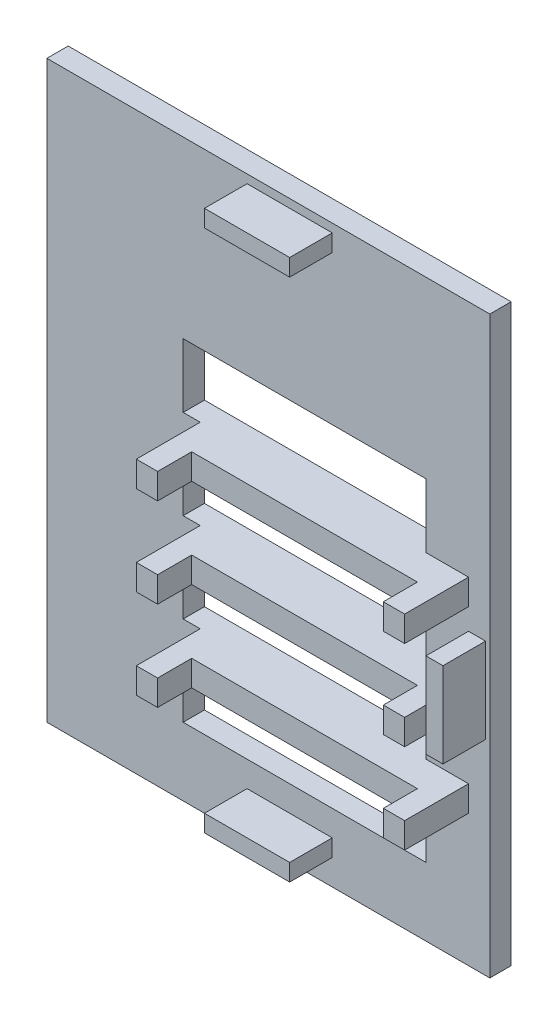
SolidWorks part; units mm, degrees
ref_plane "前基準面" through (0, 0, 0) normal (0, 0, 1) x (1, 0, 0)
ref_plane "上基準面" through (0, 0, 0) normal (0, 1, 0) x (1, 0, 0)
ref_plane "右基準面" through (0, 0, 0) normal (1, 0, 0) x (0, 0, -1)
sketch "草圖1" plane through (0, 0, 0) normal (0, 0, 1) x (1, 0, 0)
  line L17 (-17.8968, 14.4968) -> (86.1032, 14.4968)
  line L18 (-17.8968, 14.4968) -> (-17.8968, -120.5032)
  line L19 (-17.8968, -120.5032) -> (86.1032, -120.5032)
  line L20 (86.1032, 14.4968) -> (86.1032, -120.5032)
  dimension "D1" = 104
  dimension "D2" = 135
extrude "填料-伸長2" add sketch "草圖1" along normal blind 5
sketch "草圖2" plane through (0, 0, 5) normal (0, 0, 1) x (1, 0, 0)
  line L0 (86.1032, 14.4968) -> (-17.8968, 14.4968) construction
  line L1 (29.1032, 12.4968) -> (49.1032, 12.4968)
  line L2 (29.1032, 12.4968) -> (29.1032, 8.4968)
  line L3 (29.1032, 8.4968) -> (49.1032, 8.4968)
  line L4 (49.1032, 12.4968) -> (49.1032, 8.4968)
  line L10 (86.1032, -120.5032) -> (86.1032, 14.4968) construction
  line L11 (29.1032, -114.5032) -> (49.1032, -114.5032)
  line L12 (29.1032, -114.5032) -> (29.1032, -110.5032)
  line L13 (29.1032, -110.5032) -> (49.1032, -110.5032)
  line L14 (49.1032, -114.5032) -> (49.1032, -110.5032)
  line L15 (-17.8968, -120.5032) -> (86.1032, -120.5032) construction
  line L16 (-17.8968, 14.4968) -> (-17.8968, -120.5032) construction
  line L17 (85.1032, -52.5032) -> (81.1032, -52.5032)
  line L18 (85.1032, -52.5032) -> (85.1032, -72.5032)
  line L19 (85.1032, -72.5032) -> (81.1032, -72.5032)
  line L20 (81.1032, -52.5032) -> (81.1032, -72.5032)
  dimension "D2" = 20
  dimension "D3" = 4
  dimension "D4" = 67
  dimension "D5" = 4
  dimension "D6" = 20
  dimension "D7" = 20
  dimension "D8" = 4
  dimension "D9" = 6
  dimension "D10" = 47
  dimension "D11" = 2
  dimension "D12" = 1
  dimension "D13" = 47
extrude "填料-伸長3" add sketch "草圖2" along normal blind 10
sketch "草圖3" plane through (0, 0, 5) normal (0, 0, 1) x (1, 0, 0)
  line L1 (14.1032, -89.5032) -> (71.1032, -89.5032)
  line L2 (14.1032, -89.5032) -> (14.1032, -104.5032)
  line L3 (14.1032, -104.5032) -> (71.1032, -104.5032)
  line L4 (71.1032, -89.5032) -> (71.1032, -104.5032)
  line L5 (-17.8968, 14.4968) -> (-17.8968, -120.5032) construction
  line L6 (-17.8968, -120.5032) -> (86.1032, -120.5032) construction
  line L12 (14.1032, -83.5032) -> (71.1032, -83.5032)
  line L13 (14.1032, -83.5032) -> (14.1032, -68.5032)
  line L14 (14.1032, -68.5032) -> (71.1032, -68.5032)
  line L15 (71.1032, -83.5032) -> (71.1032, -68.5032)
  line L16 (14.1032, -62.5032) -> (71.1032, -62.5032)
  line L17 (14.1032, -62.5032) -> (14.1032, -47.5032)
  line L18 (14.1032, -47.5032) -> (71.1032, -47.5032)
  line L19 (71.1032, -62.5032) -> (71.1032, -47.5032)
  line L20 (14.1032, -41.5032) -> (71.1032, -41.5032)
  line L21 (14.1032, -41.5032) -> (14.1032, -26.5032)
  line L22 (14.1032, -26.5032) -> (71.1032, -26.5032)
  line L23 (71.1032, -41.5032) -> (71.1032, -26.5032)
  dimension "D1" = 16
  dimension "D2" = 15
  dimension "D3" = 57
  dimension "D4" = 32
  dimension "D5" = 6
  dimension "D6" = 15
  dimension "D7" = 6
  dimension "D8" = 6
  dimension "D9" = 15
  dimension "D10" = 15
  dimension "D11" = 57
  dimension "D12" = 57
  dimension "D13" = 57
extrude "除料-伸長1" cut sketch "草圖3" against normal up to next
sketch "草圖4" plane through (0, 0, 5) normal (0, 0, 1) x (1, 0, 0)
  line L0 (71.1032, -47.5032) -> (14.1032, -47.5032) construction
  line L1 (18.1032, -41.5032) -> (23.1032, -41.5032)
  line L2 (18.1032, -41.5032) -> (18.1032, -47.5032)
  line L3 (18.1032, -47.5032) -> (23.1032, -47.5032)
  line L4 (23.1032, -41.5032) -> (23.1032, -47.5032)
  line L10 (76.1032, -41.5032) -> (81.1032, -41.5032)
  line L11 (76.1032, -41.5032) -> (76.1032, -47.5032)
  line L12 (76.1032, -47.5032) -> (81.1032, -47.5032)
  line L13 (81.1032, -41.5032) -> (81.1032, -47.5032)
  line L14 (71.1032, -68.5032) -> (14.1032, -68.5032) construction
  line L15 (18.1032, -62.5032) -> (23.1032, -62.5032)
  line L16 (18.1032, -62.5032) -> (18.1032, -68.5032)
  line L17 (18.1032, -68.5032) -> (23.1032, -68.5032)
  line L18 (23.1032, -62.5032) -> (23.1032, -68.5032)
  line L20 (71.1032, -89.5032) -> (14.1032, -89.5032) construction
  line L21 (76.1032, -62.5032) -> (81.1032, -62.5032)
  line L22 (76.1032, -62.5032) -> (76.1032, -68.5032)
  line L23 (76.1032, -68.5032) -> (81.1032, -68.5032)
  line L24 (81.1032, -62.5032) -> (81.1032, -68.5032)
  line L25 (18.1032, -83.5032) -> (23.1032, -83.5032)
  line L26 (18.1032, -83.5032) -> (18.1032, -89.5032)
  line L27 (18.1032, -89.5032) -> (23.1032, -89.5032)
  line L28 (23.1032, -83.5032) -> (23.1032, -89.5032)
  line L29 (86.1032, -120.5032) -> (86.1032, 14.4968) construction
  line L30 (76.1032, -83.5032) -> (81.1032, -83.5032)
  line L31 (76.1032, -83.5032) -> (76.1032, -89.5032)
  line L32 (76.1032, -89.5032) -> (81.1032, -89.5032)
  line L33 (81.1032, -83.5032) -> (81.1032, -89.5032)
  point P4 (0, 0)
  point P13 (0, 0)
  dimension "D1" = 5
  dimension "D2" = 5
  dimension "D3" = 5
  dimension "D4" = 5
  dimension "D5" = 5
  dimension "D6" = 4
  dimension "D7" = 6
  dimension "D8" = 6
  dimension "D9" = 4
  dimension "D10" = 5
  dimension "D11" = 4
  dimension "D12" = 6
  dimension "D14" = 6
  dimension "D15" = 6
  dimension "D16" = 5
  dimension "D17" = 5
  dimension "D18" = 6
extrude "填料-伸長4" add sketch "草圖4" along normal blind 15
sketch "草圖6" plane through (0, 0, 5) normal (0, 0, 1) x (1, 0, 0)
  line L1 (23.1032, -41.5032) -> (76.1032, -41.5032)
  line L2 (23.1032, -41.5032) -> (23.1032, -47.5032)
  line L3 (23.1032, -47.5032) -> (76.1032, -47.5032)
  line L4 (76.1032, -41.5032) -> (76.1032, -47.5032)
  line L5 (23.1032, -62.5032) -> (76.1032, -62.5032)
  line L6 (23.1032, -62.5032) -> (23.1032, -68.5032)
  line L7 (23.1032, -68.5032) -> (76.1032, -68.5032)
  line L8 (76.1032, -62.5032) -> (76.1032, -68.5032)
  line L9 (23.1032, -83.5032) -> (76.1032, -83.5032)
  line L10 (23.1032, -83.5032) -> (23.1032, -89.5032)
  line L11 (23.1032, -89.5032) -> (76.1032, -89.5032)
  line L12 (76.1032, -83.5032) -> (76.1032, -89.5032)
  dimension "D1" = 6
  dimension "D2" = 6
  dimension "D3" = 6
extrude "填料-伸長5" add sketch "草圖6" along normal blind 7
